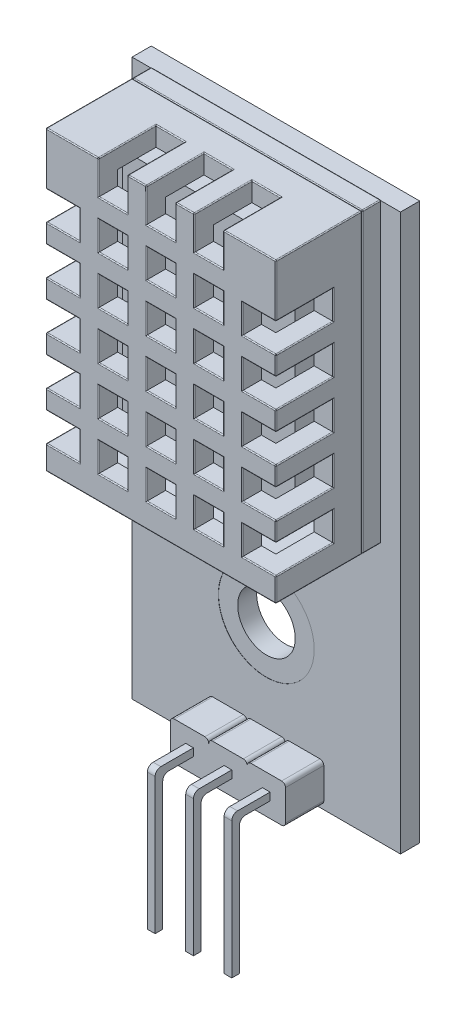
SolidWorks part; units mm, degrees
ref_plane "Front Plane" through (0, 0, 0) normal (0, 0, 1) x (1, 0, 0)
ref_plane "Top Plane" through (0, 0, 0) normal (0, 1, 0) x (1, 0, 0)
ref_plane "Right Plane" through (0, 0, 0) normal (1, 0, 0) x (0, 0, -1)
sketch "Sketch1" plane through (0, 0, 0) normal (0, 0, 1) x (1, 0, 0)
  line L1 (0, 0) -> (12, 0)
  line L2 (0, 0) -> (0, 15.5)
  line L3 (0, 15.5) -> (12, 15.5)
  line L4 (12, 0) -> (12, 15.5)
  dimension "D1" = 12
  dimension "D2" = 15.5
extrude "Boss-Extrude1" add sketch "Sketch1" along normal blind 5.5
shell "Shell2" thickness 1
sketch "Sketch3" plane through (0, 0, 5.5) normal (0, 0, 1) x (1, 0, 0)
  line L0 (12, 15.5) -> (0, 15.5) construction
  line L1 (2.75, 15.5) -> (4.25, 15.5)
  line L2 (2.75, 15.5) -> (2.75, 13.75)
  line L3 (2.75, 13.75) -> (4.25, 13.75)
  line L4 (4.25, 15.5) -> (4.25, 13.75)
  line L5 (5.25, 15.5) -> (6.75, 15.5)
  line L6 (5.25, 15.5) -> (5.25, 13.75)
  line L7 (5.25, 13.75) -> (6.75, 13.75)
  line L8 (6.75, 15.5) -> (6.75, 13.75)
  line L9 (7.75, 15.5) -> (9.25, 15.5)
  line L10 (7.75, 15.5) -> (7.75, 13.75)
  line L11 (7.75, 13.75) -> (9.25, 13.75)
  line L12 (9.25, 15.5) -> (9.25, 13.75)
  line L13 (0, 15.5) -> (0, 0) construction
  dimension "D1" = 1.5
  dimension "D2" = 1.75
  dimension "D4" = 2.75
  dimension "D3" = 3
extrude "Cut-Extrude1" cut sketch "Sketch3" against normal blind 3
sketch "Sketch4" plane through (0, 0, 5.5) normal (0, 0, 1) x (1, 0, 0)
  line L0 (2.75, 13.75) -> (4.25, 13.75) construction
  line L1 (2.75, 12.75) -> (4.25, 12.75)
  line L2 (2.75, 12.75) -> (2.75, 11.25)
  line L3 (2.75, 11.25) -> (4.25, 11.25)
  line L4 (4.25, 12.75) -> (4.25, 11.25)
  line L5 (0, 15.5) -> (0, 0) construction
  line L6 (5.25, 12.75) -> (6.75, 12.75)
  line L7 (5.25, 12.75) -> (5.25, 11.25)
  line L8 (5.25, 11.25) -> (6.75, 11.25)
  line L9 (6.75, 12.75) -> (6.75, 11.25)
  line L10 (7.75, 12.75) -> (9.25, 12.75)
  line L11 (7.75, 12.75) -> (7.75, 11.25)
  line L12 (7.75, 11.25) -> (9.25, 11.25)
  line L13 (9.25, 12.75) -> (9.25, 11.25)
  line L14 (5.25, 10.25) -> (6.75, 10.25)
  line L15 (5.25, 10.25) -> (5.25, 8.75)
  line L16 (5.25, 8.75) -> (6.75, 8.75)
  line L17 (6.75, 10.25) -> (6.75, 8.75)
  line L18 (7.75, 10.25) -> (9.25, 10.25)
  line L19 (7.75, 10.25) -> (7.75, 8.75)
  line L20 (7.75, 8.75) -> (9.25, 8.75)
  line L21 (9.25, 10.25) -> (9.25, 8.75)
  line L22 (5.25, 7.75) -> (6.75, 7.75)
  line L23 (5.25, 7.75) -> (5.25, 6.25)
  line L24 (5.25, 6.25) -> (6.75, 6.25)
  line L25 (6.75, 7.75) -> (6.75, 6.25)
  line L26 (7.75, 7.75) -> (9.25, 7.75)
  line L27 (7.75, 7.75) -> (7.75, 6.25)
  line L28 (7.75, 6.25) -> (9.25, 6.25)
  line L29 (9.25, 7.75) -> (9.25, 6.25)
  line L30 (5.25, 5.25) -> (6.75, 5.25)
  line L31 (5.25, 5.25) -> (5.25, 3.75)
  line L32 (5.25, 3.75) -> (6.75, 3.75)
  line L33 (6.75, 5.25) -> (6.75, 3.75)
  line L34 (7.75, 5.25) -> (9.25, 5.25)
  line L35 (7.75, 5.25) -> (7.75, 3.75)
  line L36 (7.75, 3.75) -> (9.25, 3.75)
  line L37 (9.25, 5.25) -> (9.25, 3.75)
  line L38 (5.25, 2.75) -> (6.75, 2.75)
  line L39 (5.25, 2.75) -> (5.25, 1.25)
  line L40 (5.25, 1.25) -> (6.75, 1.25)
  line L41 (6.75, 2.75) -> (6.75, 1.25)
  line L42 (7.75, 2.75) -> (9.25, 2.75)
  line L43 (7.75, 2.75) -> (7.75, 1.25)
  line L44 (7.75, 1.25) -> (9.25, 1.25)
  line L45 (9.25, 2.75) -> (9.25, 1.25)
  line L46 (2.75, 10.25) -> (4.25, 10.25)
  line L47 (2.75, 10.25) -> (2.75, 8.75)
  line L48 (2.75, 8.75) -> (4.25, 8.75)
  line L49 (4.25, 10.25) -> (4.25, 8.75)
  line L50 (2.75, 7.75) -> (4.25, 7.75)
  line L51 (2.75, 7.75) -> (2.75, 6.25)
  line L52 (2.75, 6.25) -> (4.25, 6.25)
  line L53 (4.25, 7.75) -> (4.25, 6.25)
  line L54 (2.75, 5.25) -> (4.25, 5.25)
  line L55 (2.75, 5.25) -> (2.75, 3.75)
  line L56 (2.75, 3.75) -> (4.25, 3.75)
  line L57 (4.25, 5.25) -> (4.25, 3.75)
  line L58 (2.75, 2.75) -> (4.25, 2.75)
  line L59 (2.75, 2.75) -> (2.75, 1.25)
  line L60 (2.75, 1.25) -> (4.25, 1.25)
  line L61 (4.25, 2.75) -> (4.25, 1.25)
  dimension "D1" = 1.5
  dimension "D2" = 1
  dimension "D3" = 2.75
  dimension "D4" = 3
  dimension "D5" = 5
extrude "Cut-Extrude2" cut sketch "Sketch4" against normal blind 3
sketch "Sketch5" plane through (0, 0, 5.5) normal (0, 0, 1) x (1, 0, 0)
  line L0 (0, 15.5) -> (0, 0) construction
  line L1 (0, 12.75) -> (1.75, 12.75)
  line L2 (0, 12.75) -> (0, 11.25)
  line L3 (0, 11.25) -> (1.75, 11.25)
  line L4 (1.75, 12.75) -> (1.75, 11.25)
  line L7 (2.75, 12.75) -> (2.75, 11.25) construction
  line L8 (10.25, 12.75) -> (12, 12.75)
  line L9 (10.25, 12.75) -> (10.25, 11.25)
  line L10 (10.25, 11.25) -> (12, 11.25)
  line L11 (12, 12.75) -> (12, 11.25)
  line L12 (10.25, 10.25) -> (12, 10.25)
  line L13 (10.25, 10.25) -> (10.25, 8.75)
  line L14 (10.25, 8.75) -> (12, 8.75)
  line L15 (12, 10.25) -> (12, 8.75)
  line L16 (10.25, 7.75) -> (12, 7.75)
  line L17 (10.25, 7.75) -> (10.25, 6.25)
  line L18 (10.25, 6.25) -> (12, 6.25)
  line L19 (12, 7.75) -> (12, 6.25)
  line L20 (10.25, 5.25) -> (12, 5.25)
  line L21 (10.25, 5.25) -> (10.25, 3.75)
  line L22 (10.25, 3.75) -> (12, 3.75)
  line L23 (12, 5.25) -> (12, 3.75)
  line L24 (10.25, 2.75) -> (12, 2.75)
  line L25 (10.25, 2.75) -> (10.25, 1.25)
  line L26 (10.25, 1.25) -> (12, 1.25)
  line L27 (12, 2.75) -> (12, 1.25)
  line L28 (0, 10.25) -> (1.75, 10.25)
  line L29 (0, 10.25) -> (0, 8.75)
  line L30 (0, 8.75) -> (1.75, 8.75)
  line L31 (1.75, 10.25) -> (1.75, 8.75)
  line L32 (0, 7.75) -> (1.75, 7.75)
  line L33 (0, 7.75) -> (0, 6.25)
  line L34 (0, 6.25) -> (1.75, 6.25)
  line L35 (1.75, 7.75) -> (1.75, 6.25)
  line L36 (0, 5.25) -> (1.75, 5.25)
  line L37 (0, 5.25) -> (0, 3.75)
  line L38 (0, 3.75) -> (1.75, 3.75)
  line L39 (1.75, 5.25) -> (1.75, 3.75)
  line L40 (0, 2.75) -> (1.75, 2.75)
  line L41 (0, 2.75) -> (0, 1.25)
  line L42 (0, 1.25) -> (1.75, 1.25)
  line L43 (1.75, 2.75) -> (1.75, 1.25)
  dimension "D1" = 1
  dimension "D2" = 2
  dimension "D3" = 5
extrude "Cut-Extrude3" cut sketch "Sketch5" against normal blind 3
sketch "Sketch6" plane through (0, 0, 0) normal (0, 0, -1) x (-1, 0, 0)
  line L4 (0, 0) -> (0, 15.5)
  line L5 (0, 15.5) -> (-12, 15.5)
  line L6 (-12, 15.5) -> (-12, 0)
  line L7 (-12, 0) -> (0, 0)
  line L8 (0, 0) -> (0, 15.5)
  line L9 (0, 15.5) -> (-12, 15.5)
  line L10 (-12, 15.5) -> (-12, 0)
  line L11 (-12, 0) -> (0, 0)
  line L12 (-1, 14.5) -> (-11, 14.5)
  line L13 (-1, 1) -> (-1, 14.5)
  line L14 (-11, 1) -> (-1, 1)
  line L15 (-11, 14.5) -> (-11, 1)
  line L16 (-1, 14.5) -> (-11, 14.5)
  line L17 (-1, 1) -> (-1, 14.5)
  line L18 (-11, 1) -> (-1, 1)
  line L19 (-11, 14.5) -> (-11, 1)
  dimension "D1" = 0
  dimension "D2" = 0
extrude "Cut-Extrude4" cut sketch "Sketch6" against normal blind 1
ref_plane "Plane1" through (0, 0, 0.99) normal (0, 0, 1) x (1, 0, 0)
sketch "Sketch8" plane through (0, 0, 0.99) normal (0, 0, 1) x (1, 0, 0)
  line L4 (0, 0) -> (12, 0)
  line L5 (0, 15.5) -> (0, 0)
  line L6 (12, 15.5) -> (0, 15.5)
  line L7 (12, 0) -> (12, 15.5)
  line L8 (0, 0) -> (12, 0)
  line L9 (0, 15.5) -> (0, 0)
  line L10 (12, 15.5) -> (0, 15.5)
  line L11 (12, 0) -> (12, 15.5)
  dimension "D1" = 0
extrude "Boss-Extrude3" add sketch "Sketch8" against normal blind 0.99 separate body
fillet "Fillet1" radius 0.05 106 edges at (6, 0, 1) (0, 12.75, 4) (0, 12, 2.5) (0, 11.25, 4) (0, 10.25, 4) (0, 9.5, 2.5) (0, 8.75, 4) (0, 7.75, 4) (0, 6.25, 4) (0, 5.25, 4) (0, 4.5, 2.5) (0, 3.75, 4) (0, 2, 2.5) (0, 0, 3.25) (0, 7.75, 1) (8.5, 15.5, 2.5) (7.75, 15.5, 4) (6.75, 15.5, 4) (6, 15.5, 2.5) (3.5, 15.5, 2.5) (2.75, 15.5, 4) (0, 15.5, 3.25) (6, 15.5, 1) (12, 1.25, 4) (12, 2, 2.5) (12, 4.5, 2.5) (12, 5.25, 4) (12, 6.25, 4) (12, 7.75, 4) (12, 8.75, 4) (12, 9.5, 2.5) (12, 12, 2.5) (12, 12.75, 4) (12, 15.5, 3.25) (12, 7.75, 1) (0.875, 3.75, 5.5) (0.875, 5.25, 5.5) (0, 5.75, 5.5) (0.875, 6.25, 5.5) (0.875, 7.75, 5.5) (0, 8.25, 5.5) (1.75, 9.5, 5.5) (0.875, 10.25, 5.5) (0.875, 11.25, 5.5) (1.75, 12, 5.5) (0, 14.125, 5.5) (1.375, 15.5, 5.5) (2.75, 14.625, 5.5) (3.5, 13.75, 5.5) (4.75, 15.5, 5.5) (5.25, 14.625, 5.5) (6, 13.75, 5.5) (7.25, 15.5, 5.5) (7.75, 14.625, 5.5) (9.25, 14.625, 5.5) (12, 14.125, 5.5) (11.125, 12.75, 5.5) (12, 10.75, 5.5) (11.125, 10.25, 5.5) (11.125, 8.75, 5.5) (12, 8.25, 5.5) (11.125, 5.25, 5.5) (11.125, 3.75, 5.5) (12, 3.25, 5.5) (11.125, 2.75, 5.5) (10.25, 2, 5.5) (6, 0, 5.5) (0, 0.625, 5.5) (0.875, 1.25, 5.5) (0.875, 2.75, 5.5) (4.25, 12, 5.5) (3.5, 12.75, 5.5) (2.75, 12, 5.5) (3.5, 11.25, 5.5) (6.75, 12, 5.5) (6, 12.75, 5.5) (5.25, 12, 5.5) (6, 11.25, 5.5) (9.25, 12, 5.5) (8.5, 12.75, 5.5) (6.75, 9.5, 5.5) (9.25, 9.5, 5.5) (8.5, 10.25, 5.5) (7.75, 9.5, 5.5) (8.5, 8.75, 5.5) (5.25, 7, 5.5) (6, 6.25, 5.5) (8.5, 7.75, 5.5) (7.75, 7, 5.5) (8.5, 6.25, 5.5) (6, 5.25, 5.5) (5.25, 4.5, 5.5) (7.75, 4.5, 5.5) (6.75, 2, 5.5) (6, 2.75, 5.5) (5.25, 2, 5.5) (8.5, 2.75, 5.5) (4.25, 9.5, 5.5) (3.5, 10.25, 5.5) (2.75, 9.5, 5.5) (3.5, 8.75, 5.5) (2.75, 7, 5.5) (3.5, 6.25, 5.5) (2.75, 4.5, 5.5) (2.75, 2, 5.5) (3.5, 1.25, 5.5)
fillet "Fillet2" radius 0.05 12 edges at (6, 15.5, 0.99) (0, 15.5, 0.495) (0, 7.75, 0.99) (0, 0, 0.495) (6, 0, 0.99) (12, 15.5, 0.495) (12, 0, 0.495) (12, 7.75, 0.99) (6, 15.5, 0) (0, 7.75, 0) (6, 0, 0) (12, 7.75, 0)
sketch "Sketch10" plane through (0, 0, 0.99) normal (0, 0, 1) x (1, 0, 0)
  line L14 (1.5, 1.5) -> (10.5, 1.5)
  line L15 (10.5, 1.5) -> (10.5, 14)
  line L16 (10.5, 14) -> (1.5, 14)
  line L17 (1.5, 14) -> (1.5, 1.5)
  line L18 (1.5, 1.5) -> (10.5, 1.5)
  line L19 (10.5, 1.5) -> (10.5, 14)
  line L20 (10.5, 14) -> (1.5, 14)
  line L21 (1.5, 14) -> (1.5, 1.5)
  dimension "D1" = 0.5
extrude "Boss-Extrude4" add sketch "Sketch10" along normal blind 2
sketch "Sketch11" plane through (0, 0, 0) normal (0, 0, -1) x (-1, 0, 0)
  line L0 (-11.95, 0.05) -> (-0.05, 0.05) construction
  line L1 (-13, 15.45) -> (1, 15.45)
  line L2 (-13, 15.45) -> (-13, -13.55)
  line L3 (-13, -13.55) -> (1, -13.55)
  line L4 (1, 15.45) -> (1, -13.55)
  point P4 (-6, 15.45)
  point P7 (-6, 0.05)
  dimension "D1" = 14
  dimension "D2" = 29
  dimension "D3" = 0
  dimension "D4" = 14
extrude "Boss-Extrude5" add sketch "Sketch11" along normal blind 1
sketch "Sketch12" plane through (0, 0, 0) normal (0, 0, 1) x (1, 0, 0)
  line L2 (3, -11.55) -> (3, -13.15)
  line L4 (9, -11.55) -> (9, -13.15)
  line L5 (13, 15.45) -> (13, -13.55) construction
  line L7 (5, -11.55) -> (5, -13.15)
  line L8 (7, -11.55) -> (7, -13.15)
  line L9 (3.2, -11.35) -> (4.8, -11.35)
  line L10 (6.8, -11.35) -> (5.2, -11.35)
  line L11 (8.8, -11.35) -> (7.2, -11.35)
  line L12 (9, -13.35) -> (9, -11.35)
  line L13 (8.8, -13.35) -> (7.2, -13.35)
  line L14 (6.8, -13.35) -> (5.2, -13.35)
  line L15 (4.8, -13.35) -> (3.2, -13.35)
  arc A0 (3, -11.55) -> (3.2, -11.35) centre (3.2, -11.55) cw
  arc A1 (5, -11.55) -> (4.8, -11.35) centre (4.8, -11.55) ccw
  arc A2 (5, -11.55) -> (5.2, -11.35) centre (5.2, -11.55) cw
  arc A3 (3.2, -13.35) -> (3, -13.15) centre (3.2, -13.15) cw
  arc A4 (4.8, -13.35) -> (5, -13.15) centre (4.8, -13.15) ccw
  arc A5 (5, -13.15) -> (5.2, -13.35) centre (5.2, -13.15) ccw
  arc A6 (7, -13.15) -> (6.8, -13.35) centre (6.8, -13.15) cw
  arc A7 (7, -13.15) -> (7.2, -13.35) centre (7.2, -13.15) ccw
  arc A8 (7, -11.55) -> (6.8, -11.35) centre (6.8, -11.55) ccw
  arc A9 (7, -11.55) -> (7.2, -11.35) centre (7.2, -11.55) cw
  arc A10 (9, -11.55) -> (8.8, -11.35) centre (8.8, -11.55) ccw
  arc A11 (9, -13.15) -> (8.8, -13.35) centre (8.8, -13.15) cw
  point P8 (3, -11.35)
  dimension "D3" = 0.2
  dimension "D5" = 0.2
  dimension "D6" = 0.2
  dimension "D8" = 0.2
  dimension "D9" = 0.2
  dimension "D10" = 0.2
  dimension "D11" = 0.2
  dimension "D12" = 0.2
  dimension "D13" = 0.2
  dimension "D14" = 0.2
  dimension "D15" = 0.2
  dimension "D16" = 0.2
  dimension "D1" = 6
  dimension "D2" = 2
  dimension "D4" = 4
  dimension "D7" = 2
extrude "Boss-Extrude6" add sketch "Sketch12" along normal blind 2 contours L15 A4 L7 A1 L9 A0 L2 A3 | L8 A8 L10 A2 L7 A5 L14 A6 | A11 L4 A10 L11 A9 L8 A7 L13
sketch "Sketch13" plane through (0, 0, 2) normal (0, 0, 1) x (1, 0, 0)
  line L0 (3.2, -11.35) -> (4.8, -11.35) construction
  line L1 (3.8, -12.1506) -> (4.2, -12.1506)
  line L2 (3.8, -12.1506) -> (3.8, -12.5494)
  line L3 (3.8, -12.5494) -> (4.2, -12.5494)
  line L4 (4.2, -12.1506) -> (4.2, -12.5494)
  line L5 (3, -11.55) -> (3, -13.15) construction
  line L6 (6.8, -11.35) -> (5.2, -11.35) construction
  line L7 (5.8, -12.1506) -> (6.2, -12.1506)
  line L8 (5.8, -12.1506) -> (5.8, -12.5494)
  line L9 (5.8, -12.5494) -> (6.2, -12.5494)
  line L10 (6.2, -12.1506) -> (6.2, -12.5494)
  line L11 (8.8, -11.35) -> (7.2, -11.35) construction
  line L12 (7.8, -12.1506) -> (8.2, -12.1506)
  line L13 (7.8, -12.1506) -> (7.8, -12.5494)
  line L14 (7.8, -12.5494) -> (8.2, -12.5494)
  line L15 (8.2, -12.1506) -> (8.2, -12.5494)
  point P4 (4, -12.1506)
  point P7 (4, -11.35)
  point P8 (3.8, -12.35)
  point P11 (3, -12.35)
  point P16 (6, -12.1506)
  point P19 (6, -11.35)
  point P24 (8, -12.1506)
  point P27 (8, -11.35)
  dimension "D1" = 0.4
  dimension "D2" = 0.3988
  dimension "D3" = 0
  dimension "D4" = 0
  dimension "D5" = 0.4
  dimension "D6" = 0
  dimension "D7" = 0.4
  dimension "D8" = 0
extrude "Boss-Extrude7" add sketch "Sketch13" along normal blind 2
sketch "Sketch14" plane through (0, -12.5494, 0) normal (0, -1, 0) x (1, 0, 0)
  line L0 (6.2, 4) -> (6.2, 2) construction
  line L1 (5.8, 4) -> (6.2, 4)
  line L2 (5.8, 4) -> (5.8, 3.5997)
  line L3 (5.8, 3.5997) -> (6.2, 3.5997)
  line L4 (6.2, 4) -> (6.2, 3.5997)
  line L5 (4.2, 4) -> (4.2, 2) construction
  line L6 (3.8, 4) -> (4.2, 4)
  line L7 (3.8, 4) -> (3.8, 3.5997)
  line L8 (3.8, 3.5997) -> (4.2, 3.5997)
  line L9 (4.2, 4) -> (4.2, 3.5997)
  line L10 (8.2, 4) -> (8.2, 2) construction
  line L11 (7.8, 4) -> (8.2, 4)
  line L12 (7.8, 4) -> (7.8, 3.5997)
  line L13 (7.8, 3.5997) -> (8.2, 3.5997)
  line L14 (8.2, 4) -> (8.2, 3.5997)
extrude "Boss-Extrude8" add sketch "Sketch14" along normal blind 7
fillet "Fillet3" radius 0.3 1 edges at (4, -12.5494, 3.5997)
fillet "Fillet4" radius 0.3 1 edges at (6, -12.5494, 3.5997)
fillet "Fillet5" radius 0.3 1 edges at (8, -12.5494, 3.5997)
fillet "Fillet6" radius 0.3 1 edges at (4, -12.1506, 4)
fillet "Fillet7" radius 0.3 1 edges at (6, -12.1506, 4)
fillet "Fillet8" radius 0.3 1 edges at (8, -12.1506, 4)
sketch "Sketch15" plane through (0, 0, 0) normal (0, 0, 1) x (1, 0, 0)
  circle A0 centre (6, -6.5668) radius 1.5
  dimension "D1" = 3
extrude "Cut-Extrude5" cut sketch "Sketch15" against normal through all
sketch "Sketch16" plane through (0, 0, 0) normal (0, 0, 1) x (1, 0, 0)
  circle A0 centre (6, -6.5668) radius 2.5
  dimension "D1" = 5
extrude "Cut-Extrude6" cut sketch "Sketch16" against normal blind 0.01
